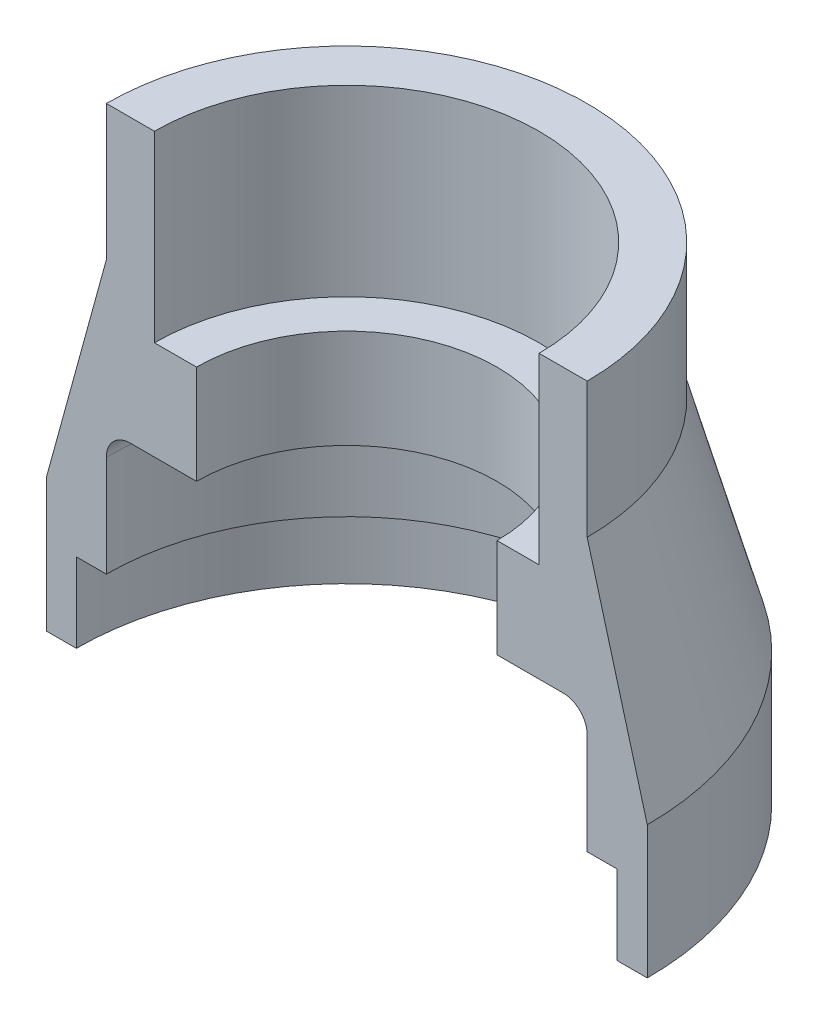
SolidWorks part; units mm, degrees
ref_plane "Front Plane" through (0, 0, 0) normal (0, 0, 1) x (1, 0, 0)
ref_plane "Top Plane" through (0, 0, 0) normal (0, 1, 0) x (1, 0, 0)
ref_plane "Right Plane" through (0, 0, 0) normal (1, 0, 0) x (0, 0, -1)
sketch "Sketch1" plane through (0, 0, 0) normal (0, 0, 1) x (1, 0, 0)
  line L0 (0, 89.6374) -> (0, -52.5006) construction
  line L1 (16, 32.8495) -> (16, 17.6091)
  line L2 (16, 17.6091) -> (12.5, 17.6091)
  line L3 (12.5, 17.6091) -> (12.5, 9.3745)
  line L4 (12.5, 9.3745) -> (18, 9.3745)
  line L5 (25, 3.3807) -> (20, 21.595)
  line L6 (20, 7.3745) -> (20, -1.0614)
  line L7 (20, -1.0614) -> (22.5, -1.0614)
  line L8 (22.5, -1.0614) -> (22.5, -7.6581)
  line L9 (20, 21.595) -> (20, 32.8495)
  line L10 (20, 32.8495) -> (16, 32.8495)
  line L11 (22.5, -7.6581) -> (25, -7.6581)
  line L12 (25, -7.6581) -> (25, 3.3807)
  arc A0 (18, 9.3745) -> (20, 7.3745) centre (18, 7.3745) cw
  dimension "D7" = 2
  dimension "D1" = 12.5
  dimension "D2" = 16
  dimension "D3" = 20
  dimension "D4" = 20
  dimension "D5" = 22.5
  dimension "D6" = 25
revolve "Revolve1" add sketch "Sketch1" angle 360 about L0
sketch "Sketch2" [suppressed] plane through (0, 0, 0) normal (0, 1, 0) x (1, 0, 0)
  line L1 (0, 0) -> (53.0318, 0)
  line L2 (0, 0) -> (0, -55.9981)
  line L3 (0, -55.9981) -> (53.0318, -55.9981)
  line L4 (53.0318, 0) -> (53.0318, -55.9981)
extrude "Cut-Extrude1" [suppressed] cut sketch "Sketch2" against normal mid plane 200
sketch "Sketch3" plane through (0, 0, 0) normal (0, 1, 0) x (1, 0, 0)
  line L1 (-36.2106, 0) -> (35.1978, 0)
  line L2 (-36.2106, 0) -> (-36.2106, -27.2755)
  line L3 (-36.2106, -27.2755) -> (35.1978, -27.2755)
  line L4 (35.1978, 0) -> (35.1978, -27.2755)
extrude "Cut-Extrude2" cut sketch "Sketch3" against normal mid plane 200
